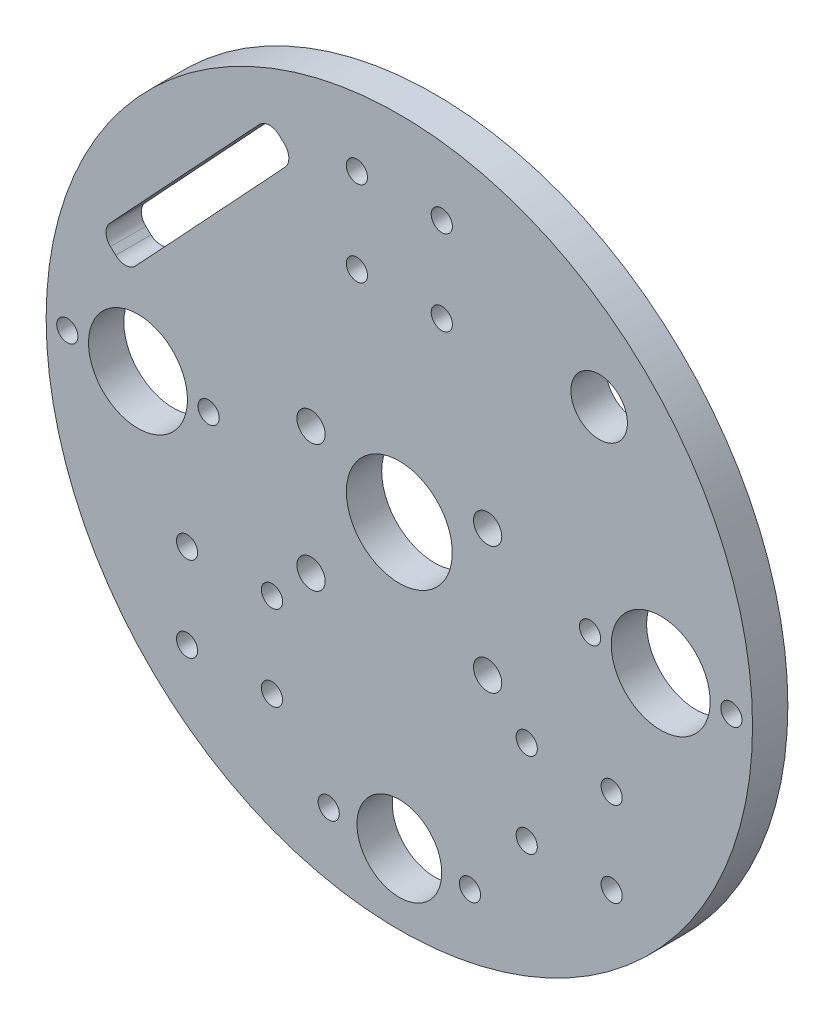
SolidWorks part; units mm, degrees
material "Acrylic (Medium-high impact)"
ref_plane "Front Plane" through (0, 0, 0) normal (0, 0, 1) x (1, 0, 0)
ref_plane "Top Plane" through (0, 0, 0) normal (0, 1, 0) x (1, 0, 0)
ref_plane "Right Plane" through (0, 0, 0) normal (1, 0, 0) x (0, 0, -1)
sketch "Sketch1" plane through (0, 0, 0) normal (0, 0, 1) x (1, 0, 0)
  circle A0 centre (0, 0) radius 50
  dimension "D1" = 100
extrude "Boss-Extrude1" add sketch "Sketch1" along normal blind 5
hole_wizard "Ø15.0 (15) Diameter Hole1" positions "Sketch3" profile "Sketch4" hole size "Ø15.0" standard "ISO" end condition through all
sketch "Sketch3" plane through (0, 0, 0) normal (0, 0, -1) x (-1, 0, 0)
  point P0 (0, 0)
sketch "Sketch4" plane through (0, 0, 0) normal (1, 0, 0) x (0, 1, 0)
  line L0 (0, 0) -> (0, 5)
  line L1 (0, 5) -> (7.5, 5)
  line L2 (7.5, 5) -> (7.5, 0)
  line L5 (7.5, 0) -> (0, 0)
  line L11 (0, -6.35) -> (0, 107.95) construction
  dimension "Thru Hole Dia." = 15
  dimension "Thru Hole Depth" = 5
hole_wizard "Ø14.0 (14) Diameter Hole1" positions "Sketch5" profile "Sketch6" hole size "Ø14.0" standard "ISO"
sketch "Sketch5" plane through (0, 0, 0) normal (0, 0, -1) x (-1, 0, 0)
  point P4 (37, 0)
  point P17 (-37, 0)
  point P18 (0, 0)
  point P21 (0, -37)
  dimension "D1" = 3
  dimension "D3" = 37
sketch "Sketch6" plane through (-37, 0, 0) normal (1, 0, 0) x (0, 1, 0)
  line L0 (0, 0) -> (0, 5)
  line L1 (0, 5) -> (7, 5)
  line L2 (7, 5) -> (7, 0)
  line L5 (7, 0) -> (0, 0)
  line L11 (0, -6.35) -> (0, 107.95) construction
  dimension "Thru Hole Dia." = 14
  dimension "Thru Hole Depth" = 5
sketch "Sketch9" plane through (0, 0, 5) normal (0, 0, 1) x (1, 0, 0)
  line L0 (0, 0) -> (0, -17.0622) construction
  circle A0 centre (12.5, 5.5) radius 2
  circle A1 centre (12.5, -12.5) radius 2
  circle A2 centre (-12.5, -12.5) radius 2
  circle A3 centre (-12.5, 5.5) radius 2
  dimension "D1" = 4
  dimension "D4" = 4
  dimension "D2" = 12.5
  dimension "D3" = 5.5
  dimension "D5" = 12.5
extrude "Cut-Extrude1" cut sketch "Sketch9" against normal blind 10
sketch "Sketch10" plane through (0, 0, 5) normal (0, 0, 1) x (1, 0, 0)
  circle A0 centre (0, -40) radius 6
  dimension "D1" = 40
  dimension "D2" = 12
extrude "Cut-Extrude2" cut sketch "Sketch10" against normal blind 10
sketch "Sketch11" plane through (0, 0, 5) normal (0, 0, 1) x (1, 0, 0)
  line L0 (0, 0) -> (24.0416, -24.0416) construction
  line L1 (0, 0) -> (24.7875, 0) construction
  line L2 (24.7875, 0) -> (63.6541, 3.2681) construction
  line L3 (63.6541, 3.2681) -> (63.3609, 2.9749) construction
  line L4 (24.0416, -24.0416) -> (30.052, -18.0312) construction
  line L5 (24.0416, -24.0416) -> (24.0416, -13.4598) construction
  circle A0 centre (24.0416, -24.0416) radius 15.5 construction
  circle A1 centre (30.052, -18.0312) radius 1.5
  circle A2 centre (30.052, -30.052) radius 1.5
  circle A3 centre (18.0312, -30.052) radius 1.5
  circle A4 centre (18.0312, -18.0312) radius 1.5
  point P19 (24.0416, -24.0416)
  dimension "D1" = 31
  dimension "D4" = 3
  dimension "D2" = 45
  dimension "D3" = 34
  dimension "D5" = 45
  dimension "D6" = 8.5
  dimension "D7" = 4
extrude "Cut-Extrude3" cut sketch "Sketch11" against normal blind 10
mirror "Mirror1" about plane through (0, 0, 0) normal (1, 0, 0) of "Cut-Extrude3"
sketch "Sketch12" plane through (0, 0, 5) normal (0, 0, 1) x (1, 0, 0)
  line L0 (0, 34) -> (6.0104, 40.0104) construction
  line L1 (0, 34) -> (0, 44.8096) construction
  circle A0 centre (0, 34) radius 15.5 construction
  circle A1 centre (6.0104, 40.0104) radius 1.5
  circle A2 centre (6.0104, 27.9896) radius 1.5
  circle A3 centre (-6.0104, 27.9896) radius 1.5
  circle A4 centre (-6.0104, 40.0104) radius 1.5
  point P15 (0, 34)
  dimension "D1" = 31
  dimension "D3" = 3
  dimension "D2" = 34
  dimension "D4" = 8.5
  dimension "D5" = 45
  dimension "D6" = 4
extrude "Cut-Extrude4" cut sketch "Sketch12" against normal blind 10
sketch "Sketch13" plane through (0, 0, 5) normal (0, 0, 1) x (1, 0, 0)
  circle A0 centre (-47, 0) radius 1.5
  circle A1 centre (-27, 0) radius 1.5
  circle A3 centre (-37, 0) radius 7 construction
  circle A4 centre (-10, -40) radius 1.5
  circle A5 centre (10, -40) radius 1.5
  circle A6 centre (27, 0) radius 1.5
  circle A7 centre (47, 0) radius 1.5
  circle A8 centre (37, 0) radius 7 construction
  circle A9 centre (0, -40) radius 6 construction
  dimension "D1" = 3
  dimension "D2" = 3
  dimension "D3" = 10
  dimension "D5" = 3
  dimension "D6" = 3
  dimension "D7" = 3
  dimension "D8" = 3
  dimension "D10" = 10
  dimension "D11" = 10
  dimension "D12" = 10
  dimension "D13" = 40
  dimension "D4" = 10
  dimension "D9" = 10
  dimension "D14" = 40
extrude "Cut-Extrude5" cut sketch "Sketch13" against normal blind 10
sketch "Sketch14" plane through (0, 0, 5) normal (0, 0, 1) x (1, 0, 0)
  line L0 (0, 0) -> (28.2843, 28.2843) construction
  line L1 (0, 0) -> (-36.7873, 0) construction
  circle A0 centre (28.2843, 28.2843) radius 4
  dimension "D1" = 8
  dimension "D2" = 40
  dimension "D3" = 135
extrude "Cut-Extrude6" cut sketch "Sketch14" against normal blind 10
sketch "Sketch15" plane through (0, 0, 5) normal (0, 0, 1) x (1, 0, 0)
  line L0 (-17.0123, 38.9334) -> (-16.2809, 38.2514)
  line L1 (-16.1822, 35.4247) -> (-37.3242, 12.7527)
  line L2 (-40.1509, 12.654) -> (-40.8822, 13.336)
  line L3 (-40.981, 16.1627) -> (-19.839, 38.8347)
  line L4 (-38.6882, 11.29) -> (-6.0772, 11.29) construction
  line L5 (0, 0) -> (-26.7532, 24.0887) construction
  arc A0 (-17.0123, 38.9334) -> (-19.839, 38.8347) centre (-18.3763, 37.4707) ccw
  arc A1 (-40.981, 16.1627) -> (-40.8822, 13.336) centre (-39.5182, 14.7987) ccw
  arc A2 (-40.1509, 12.654) -> (-37.3242, 12.7527) centre (-38.7869, 14.1167) ccw
  arc A3 (-16.2809, 38.2514) -> (-16.1822, 35.4247) centre (-17.6449, 36.7887) cw
  point P9 (-18.475, 40.2974)
  point P13 (-42.345, 14.7)
  point P19 (-14.8182, 36.8874)
  dimension "D6" = 2
  dimension "D1" = 35
  dimension "D2" = 5
  dimension "D3" = 47
  dimension "D4" = 36
  dimension "D5" = 138
extrude "Cut-Extrude7" cut sketch "Sketch15" against normal blind 10
